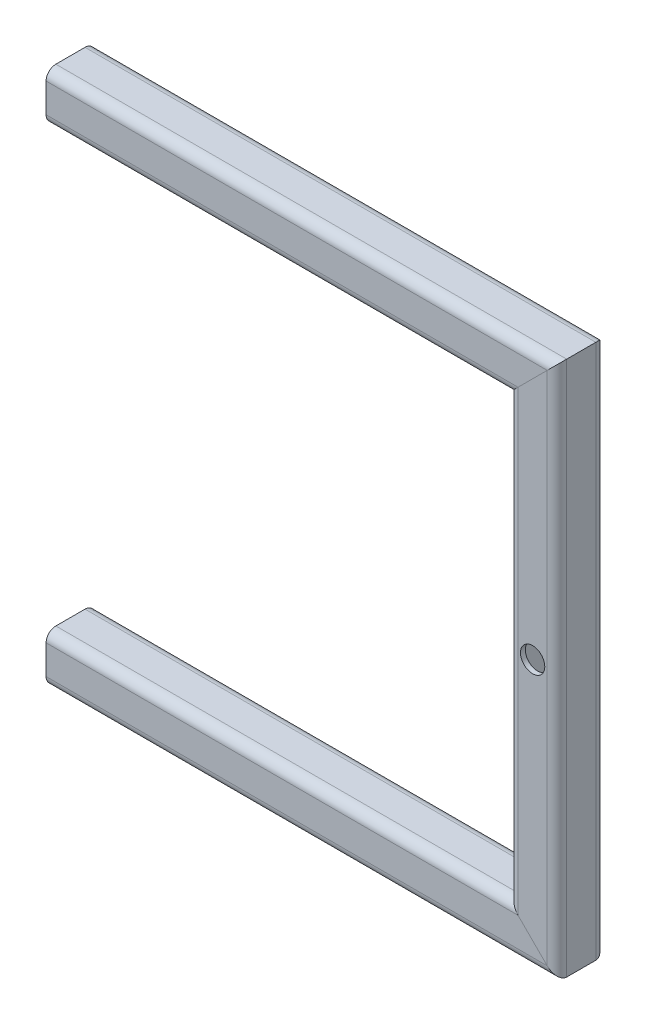
SolidWorks part; units mm, degrees
ref_plane "Front Plane" through (0, 0, 0) normal (0, 0, 1) x (1, 0, 0)
ref_plane "Top Plane" through (0, 0, 0) normal (0, 1, 0) x (1, 0, 0)
ref_plane "Right Plane" through (0, 0, 0) normal (1, 0, 0) x (0, 0, -1)
sketch "Sketch1" plane through (0, 0, 0) normal (0, 0, 1) x (1, 0, 0)
  line L5 (0, 0) -> (200, 0)
  line L7 (0, 200) -> (200, 200)
  line L8 (200, 0) -> (200, 200)
  point P0 (0, 0)
  dimension "D1" = 200
  dimension "D2" = 200
  dimension "D3" = 200
other "Square tube 20 X 20 X 2(1)"
ref_plane "Plane1" through (0, 0, 0) normal (1, 0, 0) x (0, 1, 0)
sketch "Sketch11" plane through (0, 0, 0) normal (1, 0, 0) x (0, 1, 0)
  line L0 (-6, -8) -> (6, -8)
  line L1 (-8, -6) -> (-8, 6)
  line L2 (6, 8) -> (-6, 8)
  line L3 (8, 6) -> (8, -6)
  line L4 (-6, -10) -> (6, -10)
  line L5 (-10, -6) -> (-10, 6)
  line L6 (6, 10) -> (-6, 10)
  line L7 (10, 6) -> (10, -6)
  arc A0 (10, 6) -> (6, 10) centre (6, 6) ccw
  arc A1 (6, -10) -> (10, -6) centre (6, -6) ccw
  arc A2 (-10, -6) -> (-6, -10) centre (-6, -6) ccw
  arc A3 (-6, 10) -> (-10, 6) centre (-6, 6) ccw
  arc A4 (-6, 8) -> (-8, 6) centre (-6, 6) ccw
  arc A5 (8, 6) -> (6, 8) centre (6, 6) ccw
  arc A6 (6, -8) -> (8, -6) centre (6, -6) ccw
  arc A7 (-8, -6) -> (-6, -8) centre (-6, -6) ccw
  point P0 (-10, 0)
  point P1 (10, 0)
  point P2 (0, 10)
  point P3 (0, -10)
  point P4 (0, 0)
  point P5 (-10, -10)
  point P6 (10, -10)
  point P7 (10, 10)
  point P8 (-10, 10)
  point P33 (0, 0)
  dimension "D1" = 4
  dimension "Thickness" = 2
  dimension "V_leg" = 20
sketch "Sketch12" plane through (0, 0, 0) normal (0, 0, 1) x (1, 0, 0)
  line L0 (200, 0) -> (200, 200) construction
  circle A0 centre (200, 100) radius 5
  dimension "D1" = 10
  dimension "D2" = 100
extrude "Cut-Extrude1" cut sketch "Sketch12" against normal through all and the other way through all
